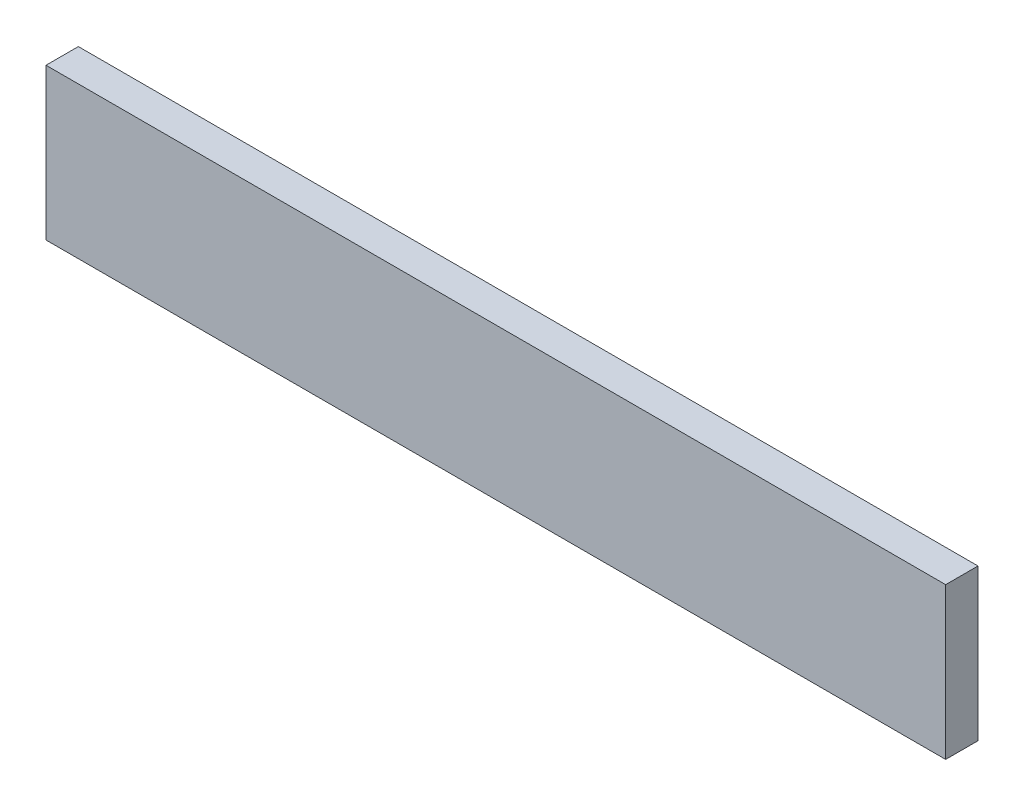
SolidWorks part; units mm, degrees
ref_plane "Plan de face" through (0, 0, 0) normal (0, 0, 1) x (1, 0, 0)
ref_plane "Plan de dessus" through (0, 0, 0) normal (0, 1, 0) x (1, 0, 0)
ref_plane "Plan de droite" through (0, 0, 0) normal (1, 0, 0) x (0, 0, -1)
sketch "Esquisse1" plane through (0, 0, 0) normal (0, 0, 1) x (1, 0, 0)
  line L1 (-19.0815, 27.0131) -> (8.7245, 27.0131)
  line L2 (-19.0815, 27.0131) -> (-19.0815, 22.3345)
  line L3 (-19.0815, 22.3345) -> (8.7245, 22.3345)
  line L4 (8.7245, 27.0131) -> (8.7245, 22.3345)
  line L5 (-19.0815, 27.0131) -> (8.7245, 22.3345) construction
  line L6 (-19.0815, 22.3345) -> (8.7245, 27.0131) construction
  point P0 (-5.1785, 24.6738)
extrude "Boss.-Extru.1" add sketch "Esquisse1" along normal blind 1
